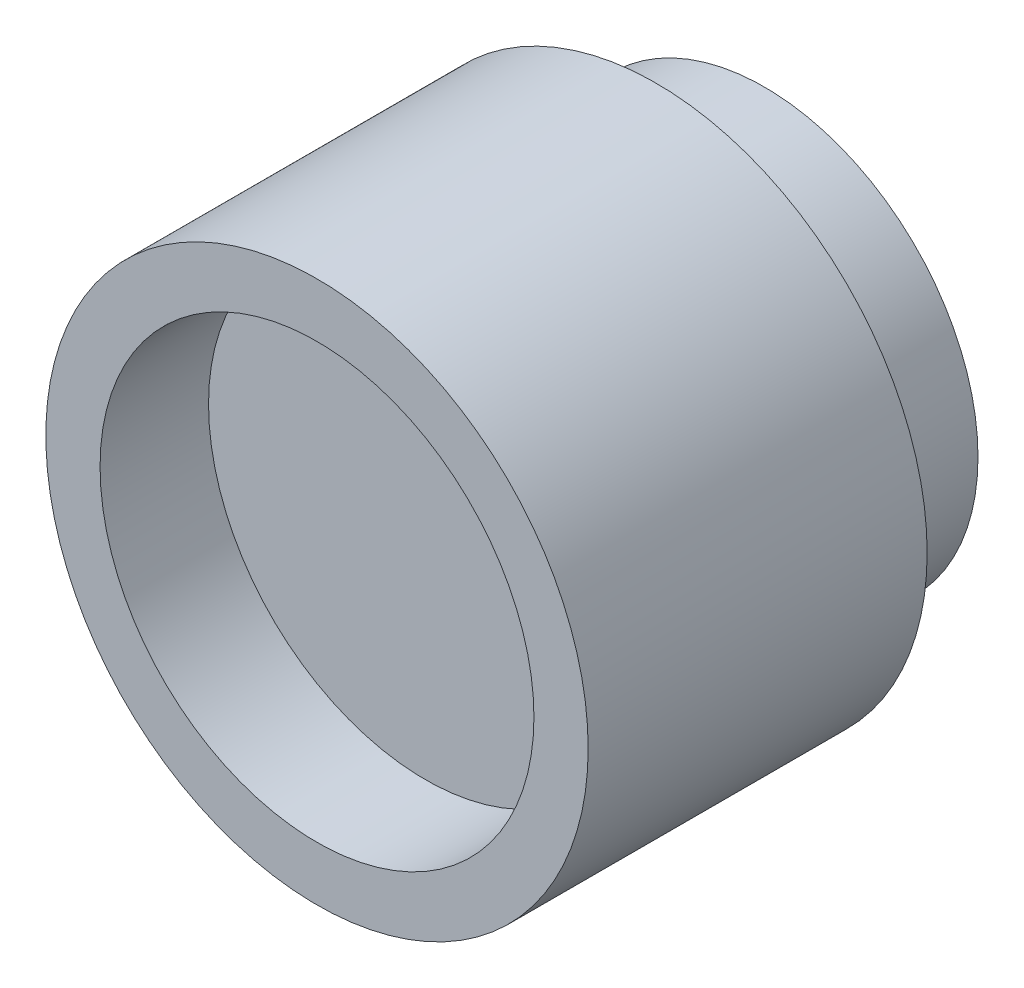
SolidWorks part; units mm, degrees
material "AISI 316 Annealed Stainless Steel Bar (SS)"
ref_plane "Front Plane" through (0, 0, 0) normal (0, 0, 1) x (1, 0, 0)
ref_plane "Top Plane" through (0, 0, 0) normal (0, 1, 0) x (1, 0, 0)
ref_plane "Right Plane" through (0, 0, 0) normal (1, 0, 0) x (0, 0, -1)
sketch "Sketch1" plane through (0, 0, 0) normal (0, 0, 1) x (1, 0, 0)
  circle A0 centre (0, 0) radius 15.75
  dimension "D1" = 31.5
extrude "Boss-Extrude1" add sketch "Sketch1" along normal blind 33
sketch "Sketch2" plane through (0, 0, 33) normal (0, 0, 1) x (1, 0, 0)
  circle A0 centre (0, 0) radius 20
  dimension "D1" = 40
extrude "Boss-Extrude2" add sketch "Sketch2" against normal offset from surface (25 mm away) 8 up to face at (15.75, 0, 0)
sketch "Sketch3" plane through (0, 0, 33) normal (0, 0, 1) x (1, 0, 0)
  circle A0 centre (0, 0) radius 16
  dimension "D1" = 32
extrude "Cut-Extrude1" cut sketch "Sketch3" against normal blind 8
